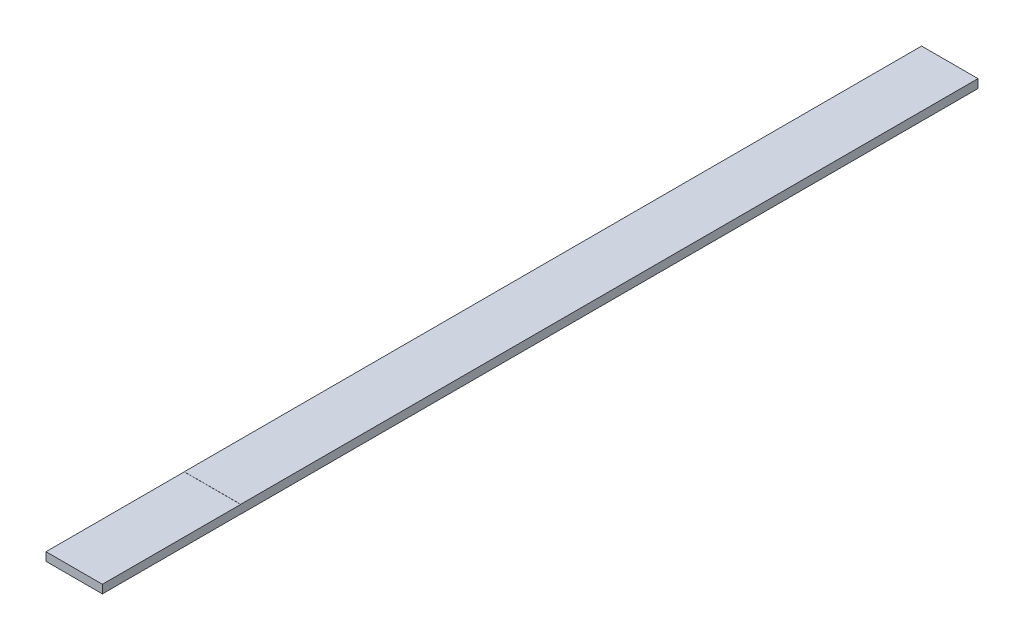
SolidWorks part; units mm, degrees
material "Ultracore Honeycomb"
ref_plane "Front Plane" through (0, 0, 0) normal (0, 0, 1) x (1, 0, 0)
ref_plane "Top Plane" through (0, 0, 0) normal (0, 1, 0) x (1, 0, 0)
ref_plane "Right Plane" through (0, 0, 0) normal (1, 0, 0) x (0, 0, -1)
sketch "Sketch2" plane through (0, 0, 0) normal (0, 0, 1) x (1, 0, 0)
  line L1 (-18, 2.75) -> (18, 2.75)
  line L2 (-18, 2.75) -> (-18, -2.75)
  line L3 (-18, -2.75) -> (18, -2.75)
  line L4 (18, 2.75) -> (18, -2.75)
  line L5 (-18, 2.75) -> (18, -2.75) construction
  line L6 (-18, -2.75) -> (18, 2.75) construction
  point P0 (0, 0)
  dimension "D1" = 36
  dimension "D2" = 5.5
extrude "Boss-Extrude1" add sketch "Sketch2" along normal blind 558.8
sketch "Sketch3" plane through (18, 0, 0) normal (1, 0, 0) x (0, 0, -1)
  line L0 (-470.55, 2.6814) -> (-470.55, -2.6814) construction
  line L1 (-558.8, -2.75) -> (-470.55, -2.75)
  line L2 (-558.8, -2.75) -> (-558.8, -2.6814)
  line L3 (-558.8, -2.6814) -> (-470.55, -2.6814)
  line L4 (-470.55, -2.75) -> (-470.55, -2.6814)
  line L5 (-558.8, 2.75) -> (-470.55, 2.75)
  line L6 (-558.8, 2.75) -> (-558.8, 2.6814)
  line L7 (-558.8, 2.6814) -> (-470.55, 2.6814)
  line L8 (-470.55, 2.75) -> (-470.55, 2.6814)
  dimension "D1" = 88.25
  dimension "D2" = 0.0686
  dimension "D3" = 0.0686
extrude "Cut-Extrude1" cut sketch "Sketch3" against normal through all
